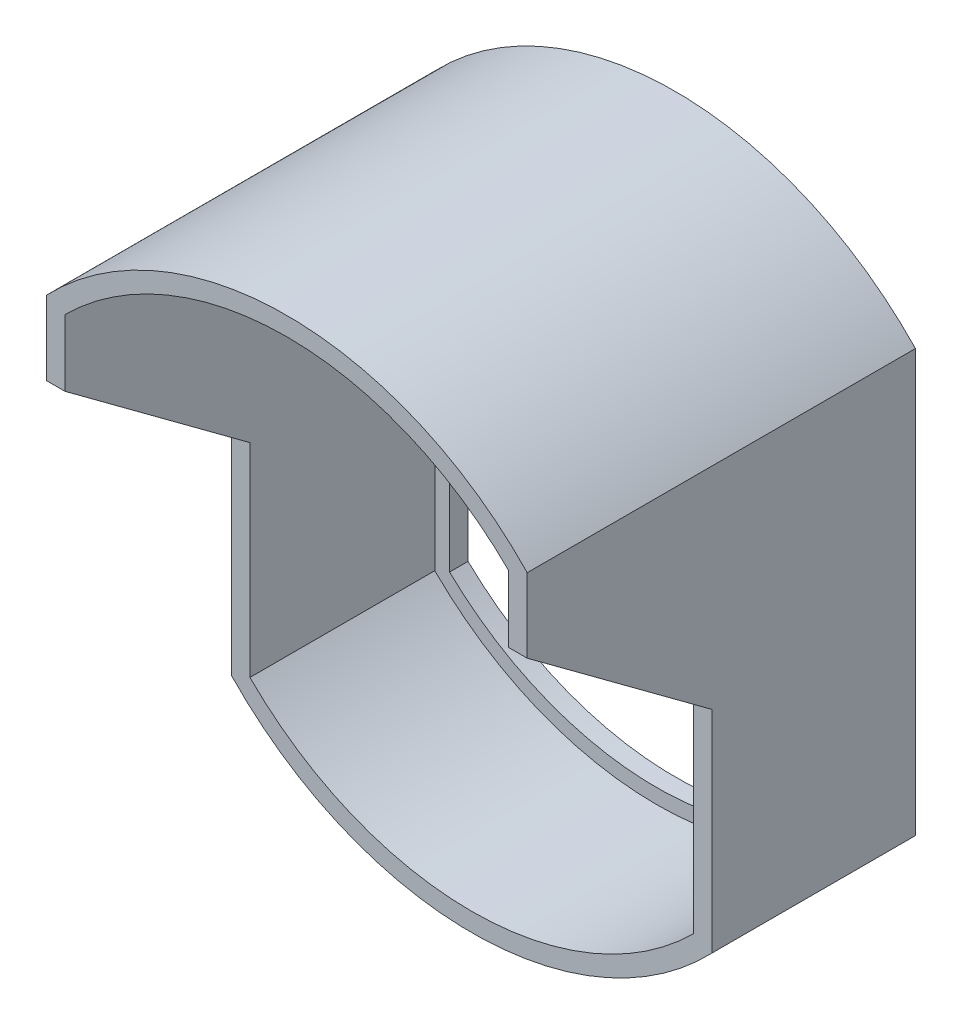
SolidWorks part; units mm, degrees
material "ABS"
ref_plane "Plano frontal" through (0, 0, 0) normal (0, 0, 1) x (1, 0, 0)
ref_plane "Plano superior" through (0, 0, 0) normal (0, 1, 0) x (1, 0, 0)
ref_plane "Plano direito" through (0, 0, 0) normal (1, 0, 0) x (0, 0, -1)
sketch "Esboço1" plane through (0, 0, 0) normal (0, 0, 1) x (1, 0, 0)
  line L0 (0, 0) -> (0, -110)
  line L1 (120, -110) -> (120, 0)
  line L2 (60, -12.6598) -> (60, -97.3402) construction
  line L3 (120, -55) -> (-37.4329, -55) construction
  line L4 (12.1875, -86.875) -> (107.8125, -86.875)
  line L5 (12.1875, -86.875) -> (12.1875, -23.125)
  line L6 (12.1875, -23.125) -> (107.8125, -23.125)
  line L7 (107.8125, -86.875) -> (107.8125, -23.125)
  line L8 (12.1875, -86.875) -> (107.8125, -23.125) construction
  line L9 (12.1875, -23.125) -> (107.8125, -86.875) construction
  arc A4 (0, 0) -> (120, 0) centre (60, -60.208) cw
  arc A5 (0, -110) -> (120, -110) centre (60, -49.792) ccw
  point P9 (60, -55)
  point P16 (0, 0)
  point P17 (60, 24.792)
  point P18 (0, 0)
  dimension "D1" = 110
  dimension "D5" = 85
  dimension "D2" = 63.75
  dimension "D3" = 95.625
extrude "Ressalto-extrusão1" add sketch "Esboço1" along normal blind 50
sketch "Esboço2" plane through (0, 0, 0) normal (0, 0, -1) x (-1, 0, 0)
  line L2 (0, 0) -> (0, -110) construction
  line L3 (-120, -110) -> (-120, 0) construction
  line L4 (-125, 2.0415) -> (-125, -112.0415)
  line L5 (5, -112.0415) -> (5, 2.0415)
  line L6 (-125, 2.0415) -> (-125, -112.0415)
  line L7 (5, -112.0415) -> (5, 2.0415)
  line L8 (0, 0) -> (0, -110)
  line L9 (-120, -110) -> (-120, 0)
  arc A2 (-120, -110) -> (0, -110) centre (-60, -49.792) ccw construction
  arc A3 (0, 0) -> (-120, 0) centre (-60, -60.208) ccw construction
  arc A4 (5, 2.0415) -> (-125, 2.0415) centre (-60, -60.208) ccw
  arc A5 (-125, -112.0415) -> (5, -112.0415) centre (-60, -49.792) ccw
  arc A6 (5, 2.0415) -> (-125, 2.0415) centre (-60, -60.208) ccw
  arc A7 (-125, -112.0415) -> (5, -112.0415) centre (-60, -49.792) ccw
  arc A8 (-120, -110) -> (0, -110) centre (-60, -49.792) ccw
  arc A9 (0, 0) -> (-120, 0) centre (-60, -60.208) ccw
  dimension "D1" = 5
extrude "Ressalto-extrusão2" add sketch "Esboço2" against normal blind 100
sketch "Esboço3" plane through (0, 0, 50) normal (0, 0, 1) x (1, 0, 0)
  line L2 (0, 0) -> (0, -110)
  line L3 (120, -110) -> (120, 0)
  line L4 (0, 0) -> (0, -110)
  line L5 (120, -110) -> (120, 0)
  arc A2 (120, 0) -> (0, 0) centre (60, -60.208) ccw
  arc A3 (0, -110) -> (120, -110) centre (60, -49.792) ccw
  arc A4 (120, 0) -> (0, 0) centre (60, -60.208) ccw
  arc A5 (0, -110) -> (120, -110) centre (60, -49.792) ccw
  dimension "D1" = 0
extrude "Corte-extrusão1" cut sketch "Esboço3" against normal blind 100
sketch "Esboço4" plane through (125, 0, 0) normal (1, 0, 0) x (0, 0, -1)
  line L0 (-100, -55) -> (-50, 2.0415) construction
  line L1 (-100, 2.0415) -> (-100, -112.0415) construction
  line L2 (-100, 2.0415) -> (0, 2.0415) construction
  line L3 (-50, 2.0415) -> (-50, -112.0415) construction
  line L4 (-100, -112.0415) -> (0, -112.0415) construction
  line L5 (-50, -55) -> (-100, -17.9941)
  line L6 (-100, -17.9941) -> (-100, -175.4935)
  line L7 (-100, -175.4935) -> (-50, -175.4935)
  line L8 (-50, -175.4935) -> (-50, -55)
extrude "Corte-extrusão2" cut sketch "Esboço4" against normal blind 169
sketch "Esboço5" plane through (0, 0, 0) normal (0, 0, -1) x (-1, 0, 0)
  line L2 (-116, -1.6845) -> (-116, -108.3155)
  line L3 (-4, -108.3155) -> (-4, -1.6845)
  line L4 (-125, 2.0415) -> (-125, -112.0415)
  line L5 (5, -112.0415) -> (5, 2.0415)
  line L6 (-125, 2.0415) -> (-125, -112.0415)
  line L7 (5, -112.0415) -> (5, 2.0415)
  arc A2 (-4, -1.6845) -> (-116, -1.6845) centre (-60, -60.208) ccw
  arc A3 (-116, -108.3155) -> (-4, -108.3155) centre (-60, -49.792) ccw
  arc A4 (5, 2.0415) -> (-125, 2.0415) centre (-60, -60.208) ccw
  arc A5 (-125, -112.0415) -> (5, -112.0415) centre (-60, -49.792) ccw
  arc A6 (5, 2.0415) -> (-125, 2.0415) centre (-60, -60.208) ccw
  arc A7 (-125, -112.0415) -> (5, -112.0415) centre (-60, -49.792) ccw
  dimension "D1" = 0
  dimension "D2" = 9
extrude "Ressalto-extrusão3" add sketch "Esboço5" along normal blind 5
